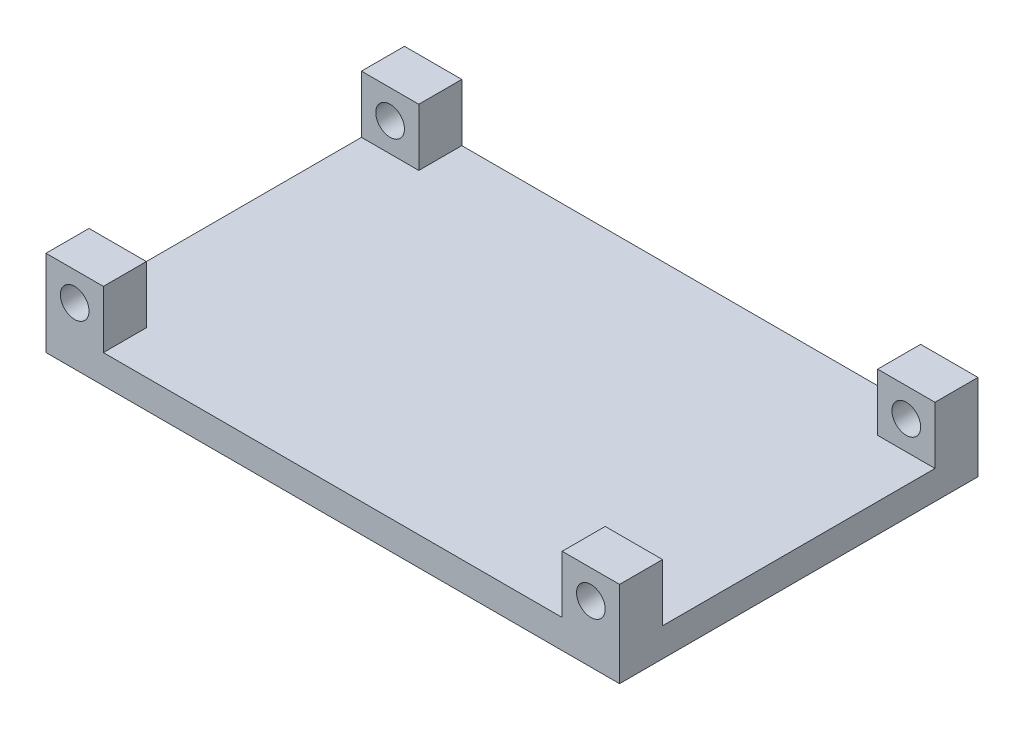
SolidWorks part; units mm, degrees
ref_plane "Front Plane" through (0, 0, 0) normal (0, 0, 1) x (1, 0, 0)
ref_plane "Top Plane" through (0, 0, 0) normal (0, 1, 0) x (1, 0, 0)
ref_plane "Right Plane" through (0, 0, 0) normal (1, 0, 0) x (0, 0, -1)
sketch "Sketch1" plane through (0, 0, 0) normal (0, 1, 0) x (1, 0, 0)
  line L1 (-200, -125) -> (200, -125)
  line L2 (-200, -125) -> (-200, 125)
  line L3 (-200, 125) -> (200, 125)
  line L4 (200, -125) -> (200, 125)
  line L5 (0, 125) -> (0, -125) construction
  line L6 (-200, 0) -> (200, 0) construction
  point P0 (0, 0)
  dimension "D1" = 400
  dimension "D2" = 250
extrude "Boss-Extrude1" add sketch "Sketch1" along normal blind 20 contours L3 L4 L1 L2
sketch "Sketch2" plane through (0, 0, 125) normal (0, 0, 1) x (1, 0, 0)
  line L1 (-200, 20) -> (-160, 20)
  line L2 (-200, 20) -> (-200, 60)
  line L3 (-200, 60) -> (-160, 60)
  line L4 (-160, 20) -> (-160, 60)
  line L5 (200, 20) -> (160, 20)
  line L6 (200, 20) -> (200, 60)
  line L7 (200, 60) -> (160, 60)
  line L8 (160, 20) -> (160, 60)
  circle A0 centre (180, 40) radius 10
  circle A1 centre (-180, 40) radius 10
  dimension "D1" = 40
extrude "Boss-Extrude2" add sketch "Sketch2" against normal blind 30
mirror "Mirror1" about plane through (0, 0, 0) normal (0, 0, 1) of "Boss-Extrude2"
